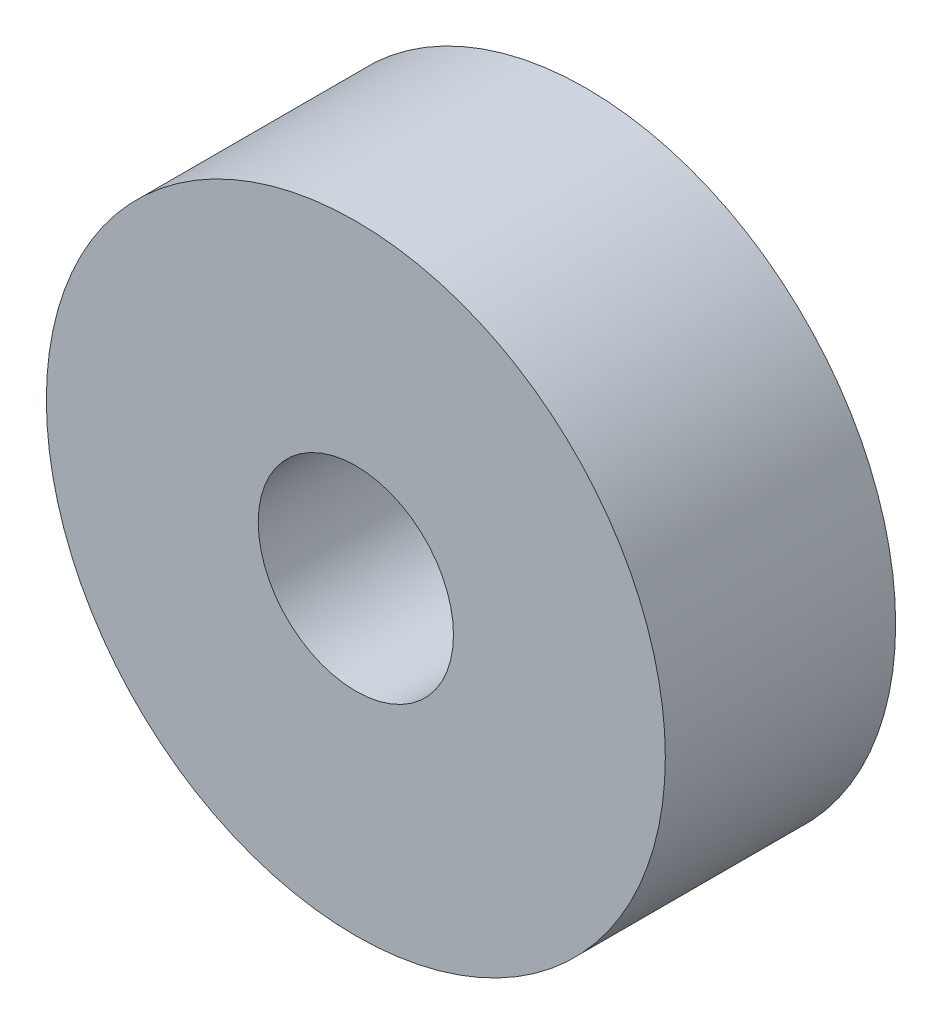
SolidWorks part; units mm, degrees
ref_plane "Front Plane" through (0, 0, 0) normal (0, 0, 1) x (1, 0, 0)
ref_plane "Top Plane" through (0, 0, 0) normal (0, 1, 0) x (1, 0, 0)
ref_plane "Right Plane" through (0, 0, 0) normal (1, 0, 0) x (0, 0, -1)
sketch "Sketch1" plane through (0, 0, 0) normal (0, 0, 1) x (1, 0, 0)
  circle A0 centre (0, 0) radius 15.0178
  circle A1 centre (0, 0) radius 4.7371
  dimension "D1" = 30.0355
  dimension "D2" = 9.4742
extrude "Boss-Extrude1" add sketch "Sketch1" along normal blind 11.176
